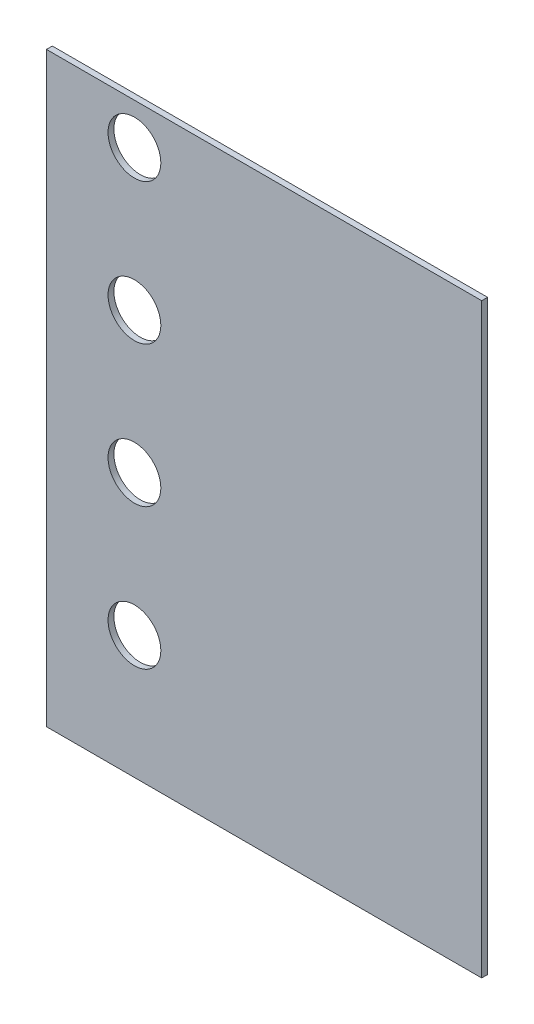
SolidWorks part; units mm, degrees
ref_plane "Front Plane" through (0, 0, 0) normal (0, 0, 1) x (1, 0, 0)
ref_plane "Top Plane" through (0, 0, 0) normal (0, 1, 0) x (1, 0, 0)
ref_plane "Right Plane" through (0, 0, 0) normal (1, 0, 0) x (0, 0, -1)
sketch "Sketch1" plane through (0, 0, 0) normal (0, 0, 1) x (1, 0, 0)
  line L1 (-123.19, -127) -> (123.19, -127)
  line L2 (-123.19, -127) -> (-123.19, 127)
  line L3 (-123.19, 127) -> (123.19, 127)
  line L4 (123.19, -127) -> (123.19, 127)
  line L5 (-123.19, -127) -> (123.19, 127) construction
  line L6 (-123.19, 127) -> (123.19, -127) construction
  point P0 (0, 0)
  dimension "D1" = 246.38
  dimension "D2" = 254
extrude "Boss-Extrude1" add sketch "Sketch1" along normal blind 2.54 contours L3 L4 L1 L2
sketch "Sketch3" plane through (0, 0, 2.54) normal (0, 0, 1) x (1, 0, 0)
  line L0 (-123.19, 127) -> (123.19, 127) construction
  line L1 (-123.19, -127) -> (-123.19, 127) construction
  circle A0 centre (-85.09, 109.22) radius 11.43
  dimension "D1" = 22.86
  dimension "D2" = 17.78
  dimension "D3" = 38.1
extrude "Cut-Extrude1" cut sketch "Sketch3" against normal through all
pattern_linear "LPattern1" count 4 spacing 60.96 along (0, -1, 0) of "Cut-Extrude1"
sketch "Sketch4" plane through (0, 0, 2.54) normal (0, 0, 1) x (1, 0, 0)
  line L0 (123.19, 127) -> (123.19, -127)
  line L1 (123.19, 127) -> (65.278, 127)
  line L2 (123.19, -127) -> (65.278, -127)
  line L3 (65.278, 127) -> (65.278, -127)
  line L4 (123.19, -127) -> (123.19, 127) construction
  line L5 (-123.19, -127) -> (123.19, -127) construction
  dimension "D1" = 57.912
extrude "Cut-Extrude2" cut sketch "Sketch4" against normal through all
sketch "Sketch5" [suppressed] plane through (0, 0, 2.54) normal (0, 0, 1) x (1, 0, 0)
  line L0 (69.088, 127) -> (69.088, -127)
  line L1 (69.088, 127) -> (48.8869, 127)
  line L2 (69.088, -127) -> (48.8869, -127)
  line L4 (69.088, 127) -> (69.088, -127) construction
